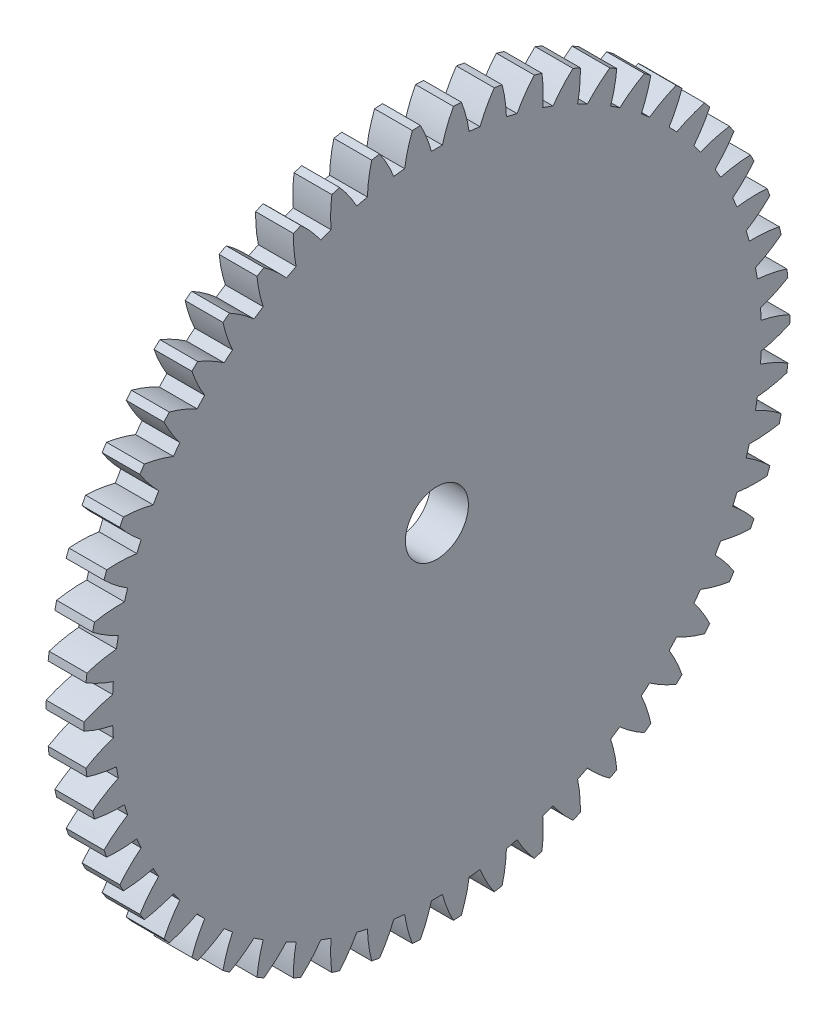
SolidWorks part; units mm, degrees
ref_plane "Plane1" through (0, 0, 0) normal (0, 0, 1) x (1, 0, 0)
ref_plane "Plane2" through (0, 0, 0) normal (0, 1, 0) x (1, 0, 0)
ref_plane "Plane3" through (0, 0, 0) normal (1, 0, 0) x (0, 0, -1)
sketch "HoldingSke" plane through (0, 0, 0) normal (0, 1, 0) x (1, 0, 0)
  line L0 (0, 0) -> (0.5878, -0.809)
  line L1 (-15, 0) -> (100, 0) construction
  line L2 (0, 0) -> (-2.1039, 2.3779)
  line L3 (0, 0) -> (-11.863, 4.5341)
  line L4 (0, 0) -> (5.0761, 6.9867)
  line L5 (0, 0) -> (-46.8476, -17.4728)
  line L6 (0, 0) -> (-2.4869, -1.6779)
  line L7 (-2.1039, 2.3779) -> (8.6586, 51.2059)
  line L8 (-76.2, 54.61) -> (-75.3, 54.61)
  line L9 (-71.009, 38.7566) -> (-53.1078, 45.2721)
  line L10 (-76.2, 71.12) -> (104.1128, 71.12)
  line L11 (0, 0) -> (-3, 0)
  line L12 (-76.2, 101.6) -> (-76.162, 101.6)
  line L13 (24.9733, 27.94) -> (52.9518, 28.4284)
  line L14 (24.9733, 27.94) -> (24.9743, 27.94)
  line L15 (24.9733, 27.94) -> (100.4006, 29.5858)
  line L16 (-63.627, -1) -> (-12.827, -1)
  circle A0 centre (0, 0) radius 2.5
  circle A1 centre (0, 0) radius 25.749
  circle A2 centre (0, 0) radius 37.5
  circle A3 centre (0, 0) radius 2.5
  dimension "MHD" = 51.498
  dimension "Hub_dia" = 75
  dimension "Bore" = 5
  dimension "MBD" = 5
  dimension "Num_teeth" = 54
  dimension "Pitch_radius" = 180.3128
  dimension "Pitch" = 1
  dimension "Width" = 3
  dimension "Overall_len" = 50
  dimension "Show_teeth" = 54
  dimension "Thickness" = 3
  dimension "OAL" = 50.0001
  dimension "T_dim" = 0.9
  dimension "Ap" = 20
  dimension "H" = 19.05
  dimension "Backlash" = 0.038
  dimension "Addendum_fac" = 1
  dimension "Dedendum_fac" = 1.25
  dimension "Clearance_fac" = 0.25
  dimension "Dedendum_add" = 0.001
  dimension "Module" = 1
sketch "BasProSke" plane through (0, 0, 0) normal (0, 1, 0) x (1, 0, 0)
  line L0 (-10, 0) -> (60, 0) construction
  line L1 (0, 0) -> (0, 28)
  line L2 (0, 0) -> (3, 0)
  line L3 (3, 0) -> (3, 28)
  line L4 (3, 28) -> (0, 28)
  dimension "Diameter" = 56
  dimension "Thickness" = 3
revolve "Base-Revolve" add sketch "BasProSke" angle 360 about L0
sketch "TooCutSke" plane through (0, 0, 0) normal (1, 0, 0) x (0, 0, -1)
  line L1 (0, 0) -> (0, 107) construction
  line L2 (0, 0) -> (-0.8518, 26.9866) construction
  line L3 (0, 0) -> (-3.1387, 53.8895) construction
  line L4 (-0.8518, 26.9866) -> (-1.5694, 26.9448) construction
  arc A0 (0.4343, 25.7453) -> (-0.4343, 25.7453) centre (0, 0) ccw
  arc A1 (1.322, 27.9942) -> (-1.322, 27.9942) centre (0, 0) ccw
  circle A2 centre (0, 0) radius 27 construction
  circle A3 centre (0, 0) radius 25.3717 construction
  arc A4 (-0.4343, 25.7453) -> (-1.322, 27.9942) centre (-10.8608, 22.9296) ccw
  arc A5 (1.322, 27.9942) -> (0.4343, 25.7453) centre (10.8608, 22.9296) ccw
  dimension "Root_dia" = 51.498
  dimension "Overcut_dia" = 56.0508
  dimension "Pitch_dia" = 54
  dimension "Base_dia" = 50.7434
  dimension "Flank_rad" = 10.8
  dimension "Half_ang" = 3.333
  dimension "Half_CT" = 0.7188
extrude "ToothCut" cut sketch "TooCutSke" along normal through all
fillet "Breaks" [suppressed] radius 0.02
fillet "RootFillets" [suppressed] radius 0.251
pattern_circular "TeethCuts" count 54 every 6.667 about axis through (-10, 0, 0) along (1, 0, 0) of "ToothCut", "RootFillets", "Breaks"
sketch "HubNeaOneSke" plane through (0, 0, 0) normal (-1, 0, 0) x (0, 0, 1)
  circle A0 centre (0, 0) radius 25.749
  dimension "Diameter" = 51.498
extrude "HubNearOne" [suppressed] add sketch "HubNeaOneSke" along normal blind 47.0001
sketch "HubNeaBotSke" plane through (0, 0, 0) normal (-1, 0, 0) x (0, 0, 1)
  circle A0 centre (0, 0) radius 25.749
  dimension "Diameter" = 51.498
extrude "HubNearBoth" [suppressed] add sketch "HubNeaBotSke" along normal blind 23.5
ref_plane "FarPln" through (3, 0, 0) normal (1, 0, 0) x (0, 0, -1)
sketch "HubFarSke" plane through (3, 0, 0) normal (1, 0, 0) x (0, 0, -1)
  circle A0 centre (0, 0) radius 25.749
  dimension "Diameter" = 51.498
extrude "HubFar" [suppressed] add sketch "HubFarSke" along normal blind 23.5
sketch "BorSke" plane through (0, 0, 0) normal (1, 0, 0) x (0, 0, -1)
  circle A0 centre (0, 0) radius 2.5
  dimension "Diameter" = 5
extrude "Bore" cut sketch "BorSke" along normal mid plane 100.0001
sketch "KeySke" plane through (0, 0, 0) normal (1, 0, 0) x (0, 0, -1)
  line L0 (-1, 0) -> (-1, 3.4)
  line L1 (-1, 3.4) -> (1, 3.4)
  line L2 (1, 3.4) -> (1, 0)
  line L3 (0, 0) -> (0, 34) construction
  line L4 (-1, 0) -> (1, 0)
  dimension "Offset" = 3.4
  dimension "Width" = 2
extrude "Keyway" [suppressed] cut sketch "KeySke" along normal mid plane 100.0001
pattern_circular "Keyway2" [suppressed] count 2 every 90 about axis through (-10, 0, 0) along (1, 0, 0)
equation "' \"Module@HoldingSke\" = 6.35"
equation "' \"Num_teeth@HoldingSke\" = 12"
equation "' \"Ap@HoldingSke\" =  20"
equation "' \"Width@HoldingSke\" = 0.5 * 25.4"
equation "' \"Hub_dia@HoldingSke\"= 1 * 25.4"
equation "' \"Overall_len@HoldingSke\" = 1.0 * 25.4"
equation "' \"Bore@HoldingSke\" = 0.75 * 25.4"
equation "' \"T_dim@HoldingSke\" = 0.1 * 25.4"
equation "' \"Width@KeySke\" = 0.25 * 25.4"
equation "' \"Show_teeth@HoldingSke\" = 13"
equation "' \"Backlash@HoldingSke\" = 0.009 * 25.4"
equation "' \"Addendum_fac@HoldingSke\" = 1.0"
equation "' \"Dedendum_fac@HoldingSke\" = 1.25"
equation "' \"Dedendum_add@HoldingSke\" = 0.00005 * 25.4"
equation "' \"Clearance_fac@HoldingSke\" = 0.25"
equation "\"Pitch@HoldingSke\" = 1 / \"Module@HoldingSke\""
equation "\"Overcut_dia@TooCutSke\" = (\"Num_teeth@HoldingSke\" + 2 * \"Addendum_fac@HoldingSke\") / \"Pitch@HoldingSke\" + 0.002 * 25.4"
equation "\"Pitch_dia@TooCutSke\" = \"Num_teeth@HoldingSke\" / \"Pitch@HoldingSke\""
equation "\"Base_dia@TooCutSke\" = \"Num_teeth@HoldingSke\" / \"Pitch@HoldingSke\" * cos((\"Ap@HoldingSke\"  * 3.14159265 / 180))"
equation "\"Root_dia@TooCutSke\" = (\"Num_teeth@HoldingSke\" + 2) / \"Pitch@HoldingSke\" - 2 * (\"Addendum_fac@HoldingSke\" + \"Dedendum_fac@HoldingSke\") / \"Pitch@HoldingSke\" - \"Dedendum_add@HoldingSke\" * 2"
equation "\"Half_ang@TooCutSke\" = 180 / \"Num_teeth@HoldingSke\""
equation "\"Half_CT@TooCutSke\" = \"Num_teeth@HoldingSke\" / \"Pitch@HoldingSke\" * sin((3.14159265 / 2 / \"Num_teeth@HoldingSke\")) / 2 - 7 * \"Backlash@HoldingSke\" / 4"
equation "\"Flank_rad@TooCutSke\" = \"Num_teeth@HoldingSke\" / \"Pitch@HoldingSke\" / 5"
equation "\"Radius@RootFillets\" = \"Clearance_fac@HoldingSke\" / \"Pitch@HoldingSke\" + \"Dedendum_add@HoldingSke\""
equation "\"Break_rad@Breaks\" = 0.02 / \"Pitch@HoldingSke\""
equation "\"Thickness@HoldingSke\" = \"Width@HoldingSke\""
equation "\"OAL@HoldingSke\" = \"Thickness@HoldingSke\""
equation "\"MHD@HoldingSke\" = (\"Num_teeth@HoldingSke\" + 2) / \"Pitch@HoldingSke\" - 2 * (\"Addendum_fac@HoldingSke\" + \"Dedendum_fac@HoldingSke\")  / \"Pitch@HoldingSke\" - \"Dedendum_add@HoldingSke\" * 2"
equation "\"MBD@HoldingSke\" = (\"Num_teeth@HoldingSke\" + 2) / \"Pitch@HoldingSke\" - 2 * (\"Addendum_fac@HoldingSke\" + \"Dedendum_fac@HoldingSke\")  / \"Pitch@HoldingSke\" - \"Dedendum_add@HoldingSke\" * 2 - 0.002 * 25.4"
equation "\"MHD@HoldingSke\" = ((sgn( \"MHD@HoldingSke\" - \"Hub_dia@HoldingSke\" )-1)*( \"MHD@HoldingSke\" - \"Hub_dia@HoldingSke\" ))/-2+ \"Hub_dia@HoldingSke\""
equation "\"MBD@HoldingSke\" = ((sgn( \"MBD@HoldingSke\" - \"Bore@HoldingSke\" )-1)*( \"MBD@HoldingSke\" - \"Bore@HoldingSke\" ))/-2+ \"Bore@HoldingSke\""
equation "\"OAL@HoldingSke\" = ((sgn( \"OAL@HoldingSke\" - \"Overall_len@HoldingSke\" )+1)*( \"OAL@HoldingSke\" - \"Overall_len@HoldingSke\" ))/2 + \"Overall_len@HoldingSke\" + 0.000002 * 25.4"
equation "\"Num_teeth@TeethCuts\" = int( \"Show_teeth@HoldingSke\" ) + 1"
equation "\"Num_teeth@TeethCuts\" = ((sgn( \"Num_teeth@TeethCuts\" - \"Num_teeth@HoldingSke\" )-1)*( \"Num_teeth@TeethCuts\" - \"Num_teeth@HoldingSke\" ))/-2+ \"Num_teeth@HoldingSke\""
equation "\"Num_teeth@TeethCuts\" = ((sgn( \"Num_teeth@TeethCuts\" - 2.0)+1)*( \"Num_teeth@TeethCuts\" - 2.0))/2 +2.0"
equation "\"Angle@TeethCuts\" = 360.0 / \"Num_teeth@HoldingSke\""
equation "\"Diameter@BasProSke\" = (\"Num_teeth@HoldingSke\" + 2 * \"Addendum_fac@HoldingSke\") / \"Pitch@HoldingSke\""
equation "\"Thickness@BasProSke\"  = \"Thickness@HoldingSke\""
equation "' \"Fillet_rad@BasProSke\" =  \"Thickness@HoldingSke\" * 0.05"
equation "\"MHD@HoldingSke\" = ((sgn( \"MHD@HoldingSke\" - \"Root_dia@TooCutSke\" )-1)*( \"MHD@HoldingSke\" - \"Root_dia@TooCutSke\" ))/-2+ \"Root_dia@TooCutSke\""
equation "\"Diameter@HubNeaOneSke\" = \"MHD@HoldingSke\""
equation "\"Length@HubNearOne\" = \"OAL@HoldingSke\" - \"Thickness@BasProSke\""
equation "\"Diameter@HubNeaBotSke\" = \"MHD@HoldingSke\""
equation "\"Length@HubNearBoth\" = ( \"OAL@HoldingSke\" - \"Thickness@BasProSke\" ) / 2.0"
equation "\"Thickness@FarPln\" = \"Thickness@BasProSke\""
equation "\"Diameter@HubFarSke\" = \"MHD@HoldingSke\""
equation "\"Length@HubFar\" = ( \"OAL@HoldingSke\" - \"Thickness@BasProSke\" ) / 2.0"
equation "\"Diameter@BorSke\" = \"MBD@HoldingSke\""
equation "\"D1@Bore\" = \"OAL@HoldingSke\" * 2.0"
equation "\"D1@Keyway\" = \"OAL@HoldingSke\" * 2.0"
equation "\"Offset@KeySke\" = \"T_dim@HoldingSke\" + \"MBD@HoldingSke\" / 2.0"
